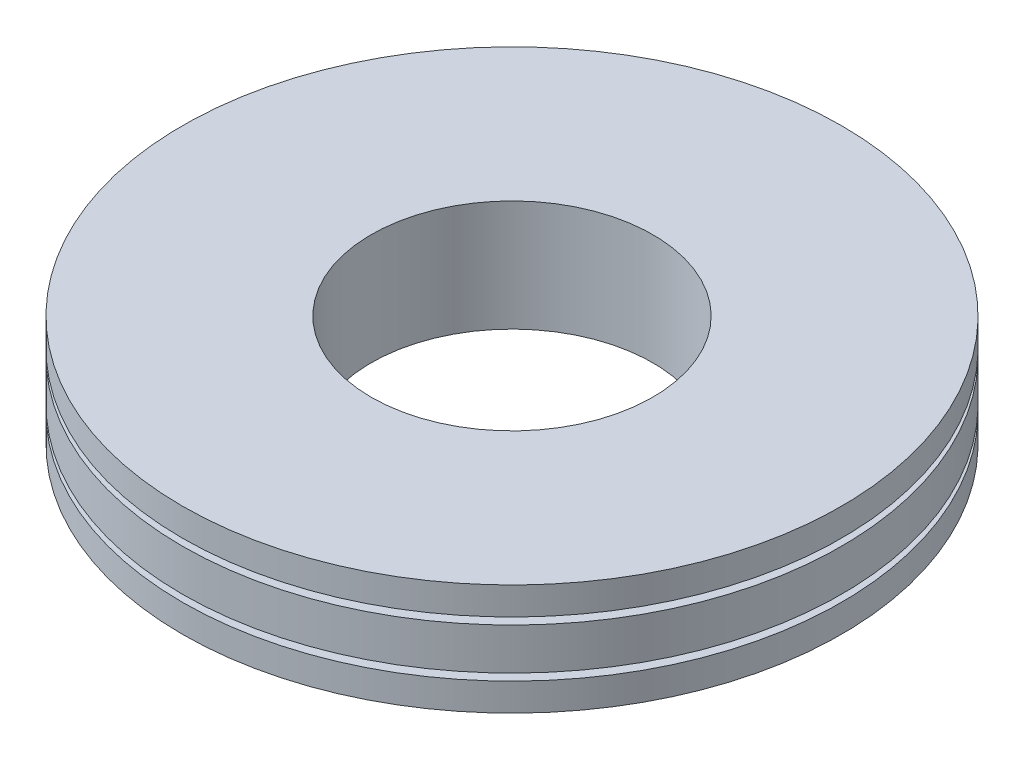
SolidWorks part; units mm, degrees
ref_plane "Front Plane" through (0, 0, 0) normal (0, 0, 1) x (1, 0, 0)
ref_plane "Top Plane" through (0, 0, 0) normal (0, 1, 0) x (1, 0, 0)
ref_plane "Right Plane" through (0, 0, 0) normal (1, 0, 0) x (0, 0, -1)
sketch "Sketch1" plane through (0, 0, 0) normal (0, 1, 0) x (1, 0, 0)
  circle A0 centre (0, 0) radius 11.875
  circle A1 centre (0, 0) radius 5.075
  dimension "D1" = 23.75
  dimension "D2" = 10.15
extrude "Boss-Extrude1" add sketch "Sketch1" along normal mid plane 4
ref_plane "Plane1" through (0, 1, 0) normal (0, 1, 0) x (1, 0, 0)
sketch "Sketch2" plane through (0, 1, 0) normal (0, 1, 0) x (1, 0, 0)
  circle A0 centre (0, 0) radius 11.875 construction
  circle A1 centre (0, 0) radius 11.875
  circle A2 centre (0, 0) radius 11.375
  dimension "D1" = 0.5
extrude "Cut-Extrude1" cut sketch "Sketch2" against normal blind 0.25
mirror "Mirror1" about plane through (0, 0, 0) normal (0, 1, 0) of "Cut-Extrude1"
